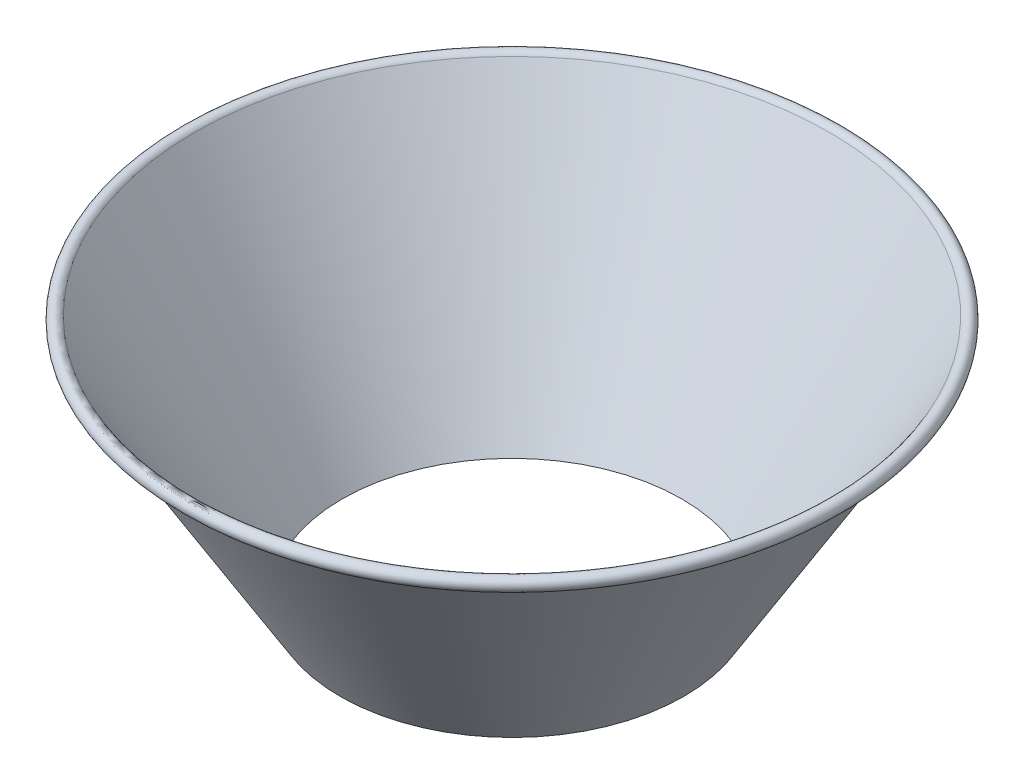
SolidWorks part; units mm, degrees
ref_plane "Front Plane" through (0, 0, 0) normal (0, 0, 1) x (1, 0, 0)
ref_plane "Top Plane" through (0, 0, 0) normal (0, 1, 0) x (1, 0, 0)
ref_plane "Right Plane" through (0, 0, 0) normal (1, 0, 0) x (0, 0, -1)
sketch "Sketch1" plane through (0, 0, 0) normal (0, 0, 1) x (1, 0, 0)
  line L0 (0, 76.2) -> (0, -76.2) construction
  line L1 (-73.025, 76.2) -> (73.025, 76.2) construction
  line L2 (-12.065, -19.05) -> (12.065, -19.05) construction
  line L3 (-6.35, -76.2) -> (6.35, -76.2) construction
  line L5 (25.4, 91.852) -> (-25.4, 91.852) construction
  line L6 (25.4, 91.852) -> (25.4, -21.9495) construction
  line L7 (25.4, -21.9495) -> (-25.4, -21.9495) construction
  line L8 (-25.4, 91.852) -> (-25.4, -21.9495) construction
  line L9 (25.4, 91.852) -> (-25.4, -21.9495) construction
  line L10 (25.4, -21.9495) -> (-25.4, 91.852) construction
  point P0 (0, 34.9513)
  point P4 (0, 0)
  point P8 (0, 76.2)
  point P11 (0, -19.05)
  point P14 (0, -76.2)
  point P18 (0, 0)
  dimension "Top OD" = 146.05
  dimension "Height" = 152.4
  dimension "Spout Length" = 57.15
  dimension "Spout OD" = 12.7
  dimension "Spout Top Diameter" = 24.13
  dimension "D1" = 50.8
sketch "Sketch3" plane through (0, 0, 0) normal (0, 0, 1) x (1, 0, 0)
  line L0 (-73.025, 74.7395) -> (-73.025, 76.2) construction
  line L1 (-73.025, 76.2) -> (73.025, 76.2) construction
  line L6 (-71.5645, 73.279) -> (-71.5645, 73.66)
  line L7 (-13.6525, -19.05) -> (13.6525, -19.05) construction
  line L9 (-12.065, -19.05) -> (-6.35, -76.2) construction
  line L10 (-6.35, -76.2) -> (-5.9671, -76.2) construction
  line L11 (-6.35, -76.2) -> (6.35, -76.2) construction
  line L12 (-5.9671, -76.2) -> (-11.6821, -19.05) construction
  line L16 (-12.065, -19.05) -> (-12.1031, -18.669)
  line L17 (-12.1031, -18.669) -> (-13.4375, -18.669)
  line L18 (-13.4375, -18.669) -> (-70.3144, 75.4946)
  line L19 (-13.6525, -19.05) -> (-70.1319, 74.4556)
  line L20 (-70.1319, 74.4556) -> (-70.6405, 75.2976)
  line L21 (-12.065, -19.05) -> (-13.6525, -19.05)
  circle A0 centre (-71.5645, 74.7395) radius 1.4605 construction
  arc A1 (-71.5645, 73.279) -> (-70.3144, 75.4946) centre (-71.5645, 74.7395) cw
  circle A3 centre (-71.5645, 74.7395) radius 1.0795 construction
  arc A4 (-71.5645, 73.66) -> (-70.6405, 75.2976) centre (-71.5645, 74.7395) cw
  point P21 (0, -19.05)
  dimension "D1" = 2.921
  dimension "D3" = 0.381
  dimension "D4" = 0.381
  dimension "D5" = 0.381
  dimension "D6" = 0.381
  dimension "D2" = 1.5875
revolve "Revolve1" add sketch "Sketch3" angle 360 about L0
sketch "Sketch4" plane through (0, 0, 0) normal (0, 0, 1) x (1, 0, 0)
  line L0 (-5.9671, -76.2) -> (-11.6821, -19.05) construction
  line L1 (-12.065, -19.05) -> (-6.35, -76.2) construction
  line L2 (-5.9671, -76.2) -> (-11.6821, -19.05)
  line L3 (-12.065, -19.05) -> (-6.35, -76.2)
  line L4 (-5.9671, -76.2) -> (-6.35, -76.2)
  line L5 (-12.065, -19.05) -> (-12.1031, -18.669)
  line L6 (-12.1031, -18.669) -> (-13.4375, -18.669)
  line L7 (-13.4375, -18.669) -> (-13.6355, -18.3412)
  line L8 (-13.4375, -18.669) -> (-70.3144, 75.4946) construction
  line L9 (-13.6355, -18.3412) -> (-11.753, -18.3412)
  line L10 (-11.753, -18.3412) -> (-11.6821, -19.05)
revolve "Revolve2" add sketch "Sketch4" angle 360 about L0
fillet "Fillet1" radius 2.54 1 edges at (-13.6525, -19.05, 0)
sketch "Sketch9" plane through (0, 0, 0) normal (0, 0, 1) x (1, 0, 0)
  line L0 (0, 0) -> (0, 76.2) construction
  line L1 (71.5645, 76.2) -> (-71.5645, 76.2) construction
  line L4 (-73.025, 76.2) -> (73.025, 76.2)
  line L5 (-6.35, -76.2) -> (6.35, -76.2)
  line L6 (12.065, -19.05) -> (-12.065, -19.05)
  point P8 (12.065, -19.05)
  point P11 (0, 76.2)
  point P14 (0, -76.2)
  point P17 (0, -19.05)
  point P18 (-73.025, 76.2)
  point P19 (-12.065, -19.05)
  point P20 (-6.35, -76.2)
  point P21 (6.35, -76.2)
  dimension "D1" = 12.7
  dimension "D2" = 24.13
  dimension "D4" = 146.05
sketch "Sketch11" plane through (0, 0, 0) normal (0, 0, 1) x (1, 0, 0)
  line L0 (-24.6831, 76.2) -> (-24.6831, 21.445) construction
  line L5 (71.5645, 76.2) -> (-71.5645, 76.2) construction
  line L6 (14.3935, -17.8232) -> (70.6405, 75.2976) construction
  line L7 (38.1123, 21.445) -> (-38.0877, 21.445)
  line L8 (38.1123, 21.445) -> (38.1123, -92.855)
  line L9 (38.1123, -92.855) -> (-38.0877, -92.855)
  line L10 (-38.0877, 21.445) -> (-38.0877, -92.855)
  line L11 (38.1123, 21.445) -> (-38.0877, -92.855) construction
  line L12 (38.1123, -92.855) -> (-38.0877, 21.445) construction
  point P0 (0.0123, -35.705)
  point P5 (0, 0)
  dimension "D1" = 76.2
  dimension "D2" = 114.3
  dimension "D3" = 54.755
extrude "Cut-Extrude1" cut sketch "Sketch11" against normal through all both and the other way through all
equation "\"D4@Sketch3\" = \"D3@Sketch3\""
equation "\"D5@Sketch3\" = \"D3@Sketch3\""
equation "\"D6@Sketch3\" = \"D3@Sketch3\""
equation "\"D1@Sketch9\" = \"Spout OD@Sketch1\""
equation "\"D2@Sketch9\" = \"Spout Top Diameter@Sketch1\""
equation "\"D4@Sketch9\" = \"Top OD@Sketch1\""
equation "\"Spout Top Diameter@Sketch1\"=\"Spout OD@Sketch1\"*1.9"
